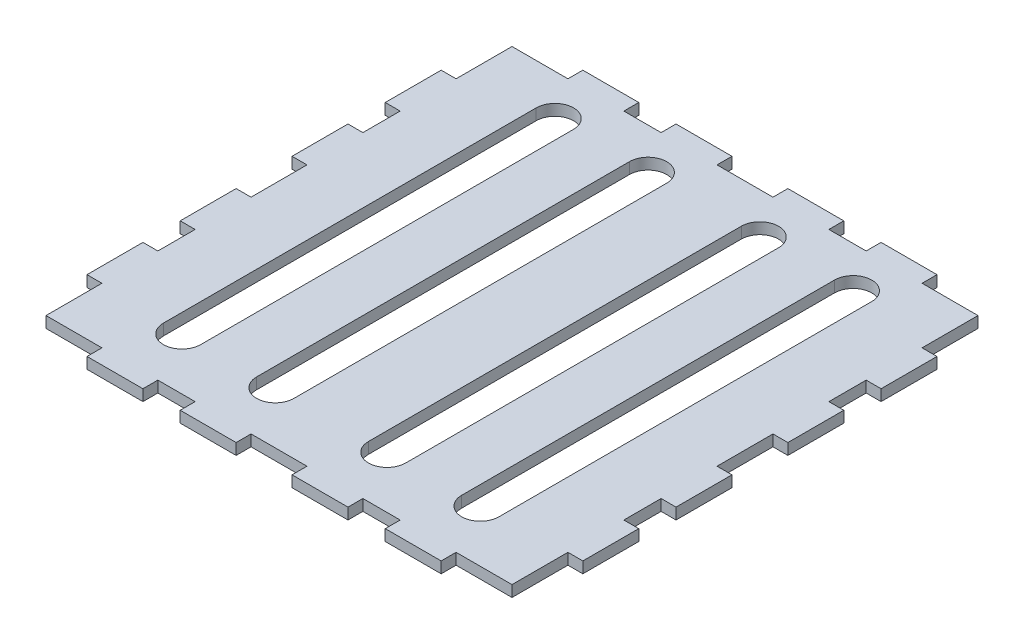
SolidWorks part; units mm, degrees
material "Oak"
ref_plane "Front Plane" through (0, 0, 0) normal (0, 0, 1) x (1, 0, 0)
ref_plane "Top Plane" through (0, 0, 0) normal (0, 1, 0) x (1, 0, 0)
ref_plane "Right Plane" through (0, 0, 0) normal (1, 0, 0) x (0, 0, -1)
sketch "Sketch1" plane through (0, 0, 0) normal (0, 1, 0) x (1, 0, 0)
  line L0 (0, 80.1692) -> (0, -87.0923) construction
  line L5 (-66.5, 46) -> (-66.5, 31)
  line L8 (-7.5, 65) -> (-7.5, 61)
  line L12 (-7.5, -68) -> (-7.5, -64)
  line L15 (-40, 78.4584) -> (-40, -95.43) construction
  line L16 (-32.5, 61) -> (-22.5, 61)
  line L17 (-22.5, 61) -> (-22.5, 65)
  line L18 (-32.5, 61) -> (-32.5, 65)
  line L20 (-57.5, 61) -> (-47.5, 61)
  line L21 (-47.5, 61) -> (-47.5, 65)
  line L22 (-47.5, 65) -> (-32.5, 65)
  line L23 (-22.5, 65) -> (-7.5, 65)
  line L35 (-22.5, -64) -> (-22.5, -68)
  line L36 (-32.5, -64) -> (-22.5, -64)
  line L37 (-32.5, -64) -> (-32.5, -68)
  line L39 (-47.5, -64) -> (-47.5, -68)
  line L40 (-57.5, -64) -> (-47.5, -64)
  line L41 (-22.5, -68) -> (-7.5, -68)
  line L42 (-47.5, -68) -> (-32.5, -68)
  line L69 (-62.5, -49) -> (-62.5, -59)
  line L70 (-66.5, -49) -> (-62.5, -49)
  line L71 (-62.5, -34) -> (-66.5, -34)
  line L72 (-62.5, -24) -> (-62.5, -34)
  line L73 (-66.5, -24) -> (-62.5, -24)
  line L74 (-66.5, -9) -> (-62.5, -9)
  line L75 (-62.5, -9) -> (-62.5, 6)
  line L76 (-62.5, 6) -> (-66.5, 6)
  line L80 (-66.5, 46) -> (-62.5, 46)
  line L81 (-62.5, 46) -> (-62.5, 56)
  line L87 (-14.7774, 72.9742) -> (-14.7774, -82.3113) construction
  line L89 (-66.5, -9) -> (-66.5, -24)
  line L94 (-66.5, 21) -> (-66.5, 6)
  line L96 (-66.5, -34) -> (-66.5, -49)
  line L97 (-40, 50) -> (-40, -50) construction
  line L100 (-35, 50) -> (-35, -50)
  line L101 (-45, 50) -> (-45, -50)
  line L102 (-15, 50) -> (-15, -50) construction
  line L103 (-10, 50) -> (-10, -50)
  line L104 (-20, 50) -> (-20, -50)
  line L105 (-7.5, -64) -> (7.5, -64)
  line L108 (-7.5, 61) -> (7.5, 61)
  line L111 (-57.5, -64) -> (-62.5, -64)
  line L112 (-62.5, -64) -> (-62.5, -59)
  line L113 (-62.5, 56) -> (-62.5, 61)
  line L114 (-62.5, 61) -> (-57.5, 61)
  line L115 (-66.5, 21) -> (-62.5, 21)
  line L116 (-62.5, 21) -> (-62.5, 31)
  line L117 (-62.5, 31) -> (-66.5, 31)
  line L119 (14.7774, 72.9742) -> (14.7774, -82.3113) construction
  line L120 (40, 78.4584) -> (40, -95.43) construction
  line L121 (62.5, 31) -> (66.5, 31)
  line L122 (62.5, 21) -> (62.5, 31)
  line L123 (66.5, 21) -> (62.5, 21)
  line L124 (62.5, 61) -> (57.5, 61)
  line L125 (62.5, 56) -> (62.5, 61)
  line L126 (62.5, -64) -> (62.5, -59)
  line L127 (57.5, -64) -> (62.5, -64)
  line L128 (66.5, -34) -> (66.5, -49)
  line L129 (66.5, 21) -> (66.5, 6)
  line L130 (66.5, -9) -> (66.5, -24)
  line L131 (62.5, 46) -> (62.5, 56)
  line L132 (66.5, 46) -> (62.5, 46)
  line L133 (62.5, 6) -> (66.5, 6)
  line L134 (62.5, -9) -> (62.5, 6)
  line L135 (66.5, -9) -> (62.5, -9)
  line L136 (66.5, -24) -> (62.5, -24)
  line L137 (62.5, -24) -> (62.5, -34)
  line L138 (62.5, -34) -> (66.5, -34)
  line L139 (66.5, -49) -> (62.5, -49)
  line L140 (62.5, -49) -> (62.5, -59)
  line L141 (47.5, -68) -> (32.5, -68)
  line L142 (22.5, -68) -> (7.5, -68)
  line L143 (57.5, -64) -> (47.5, -64)
  line L144 (47.5, -64) -> (47.5, -68)
  line L145 (32.5, -64) -> (32.5, -68)
  line L146 (32.5, -64) -> (22.5, -64)
  line L147 (22.5, -64) -> (22.5, -68)
  line L148 (22.5, 65) -> (7.5, 65)
  line L149 (47.5, 65) -> (32.5, 65)
  line L150 (47.5, 61) -> (47.5, 65)
  line L151 (57.5, 61) -> (47.5, 61)
  line L152 (32.5, 61) -> (32.5, 65)
  line L153 (22.5, 61) -> (22.5, 65)
  line L154 (32.5, 61) -> (22.5, 61)
  line L155 (7.5, -68) -> (7.5, -64)
  line L156 (7.5, 65) -> (7.5, 61)
  line L157 (66.5, 46) -> (66.5, 31)
  line L158 (15, 50) -> (15, -50) construction
  line L159 (10, 50) -> (10, -50)
  line L160 (20, 50) -> (20, -50)
  line L161 (40, 50) -> (40, -50) construction
  line L162 (35, 50) -> (35, -50)
  line L163 (45, 50) -> (45, -50)
  arc A0 (-35, 50) -> (-45, 50) centre (-40, 50) ccw
  arc A1 (-45, -50) -> (-35, -50) centre (-40, -50) ccw
  arc A2 (-10, 50) -> (-20, 50) centre (-15, 50) ccw
  arc A3 (-20, -50) -> (-10, -50) centre (-15, -50) ccw
  arc A4 (10, 50) -> (20, 50) centre (15, 50) cw
  arc A5 (20, -50) -> (10, -50) centre (15, -50) cw
  arc A6 (35, 50) -> (45, 50) centre (40, 50) cw
  arc A7 (45, -50) -> (35, -50) centre (40, -50) cw
  point P1 (-64.5, -9)
  point P39 (0, 61)
  point P40 (0, -64)
  point P91 (-40, -68)
  point P94 (-40, 0)
  point P99 (-35, 0)
  point P100 (-40, 65)
  point P101 (15, 0)
  point P105 (-15, 0)
  point P115 (40, 0)
  dimension "D4" = 62.5
  dimension "D5" = 15
  dimension "D6" = 62.5
  dimension "D7" = 10
  dimension "D8" = 62.5
  dimension "D9" = 15
  dimension "D10" = 15
  dimension "D11" = 10
  dimension "D12" = 15
  dimension "D13" = 10
  dimension "D14" = 15
  dimension "D15" = 4
  dimension "D16" = 4
  dimension "D17" = 15
  dimension "D19" = 62.5
  dimension "D20" = 4
  dimension "D23" = 15
  dimension "D26" = 15
  dimension "D31" = 100
  dimension "D32" = 10
  dimension "D33" = 2
  dimension "D34" = 15
  dimension "D35" = 15
  dimension "D36" = 15
  dimension "D37" = 125
  dimension "D39" = 4
extrude "Boss-Extrude1" add sketch "Sketch1" along normal blind 3
